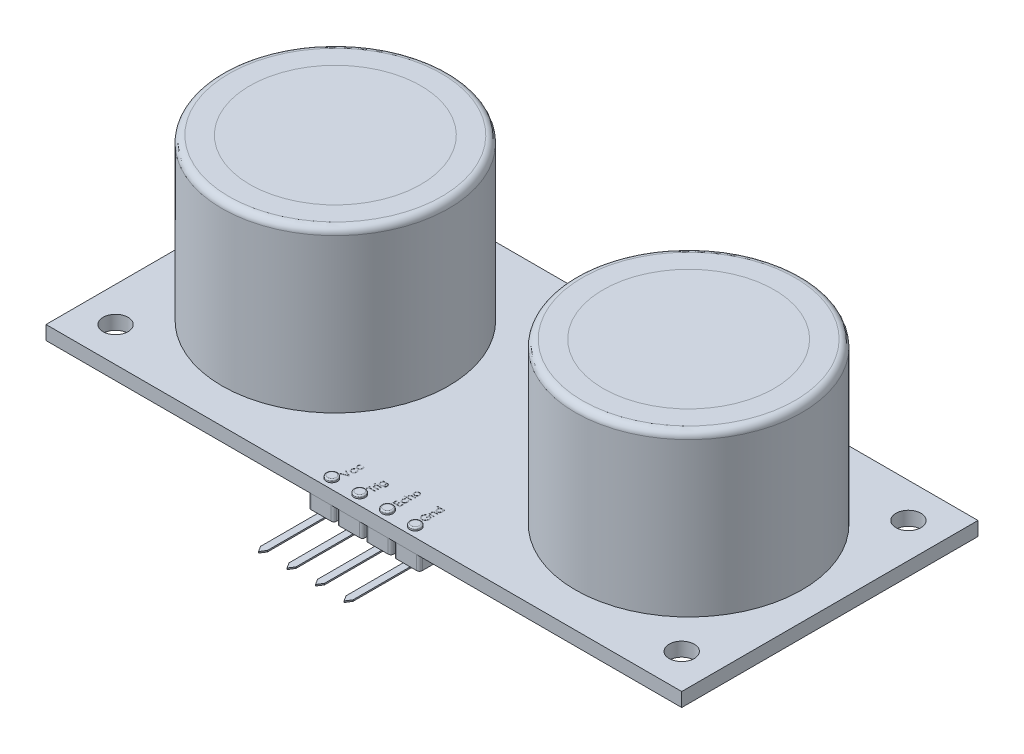
SolidWorks part; units mm, degrees
ref_plane "Front Plane" through (0, 0, 0) normal (0, 0, 1) x (1, 0, 0)
ref_plane "Top Plane" through (0, 0, 0) normal (0, 1, 0) x (1, 0, 0)
ref_plane "Right Plane" through (0, 0, 0) normal (1, 0, 0) x (0, 0, -1)
sketch "Sketch1" plane through (0, 0, 0) normal (0, 1, 0) x (1, 0, 0)
  line L1 (22.85, -10.65) -> (-22.85, -10.65)
  line L2 (22.85, -10.65) -> (22.85, 10.65)
  line L3 (22.85, 10.65) -> (-22.85, 10.65)
  line L4 (-22.85, -10.65) -> (-22.85, 10.65)
  line L5 (22.85, -10.65) -> (-22.85, 10.65) construction
  line L6 (22.85, 10.65) -> (-22.85, -10.65) construction
  line L7 (-20.35, -8.15) -> (20.35, -8.15) construction
  line L8 (-20.35, -8.15) -> (-20.35, 8.15) construction
  line L9 (-20.35, 8.15) -> (20.35, 8.15) construction
  line L10 (20.35, -8.15) -> (20.35, 8.15) construction
  circle A0 centre (20.35, 8.15) radius 0.9
  circle A1 centre (-20.35, -8.15) radius 0.9
  circle A2 centre (-20.35, 8.15) radius 0.9
  circle A3 centre (20.35, -8.15) radius 0.9
  point P0 (0, 0)
  dimension "D3" = 1.8
  dimension "D1" = 45.7
  dimension "D2" = 21.3
  dimension "D4" = 2.5
  dimension "D5" = 2.5
  dimension "D6" = 2.5
  dimension "D7" = 2.5
extrude "Boss-Extrude1" add sketch "Sketch1" along normal blind 1
sketch "Sketch2" plane through (0, 1, 0) normal (0, 1, 0) x (1, 0, 0)
  line L0 (0, 0) -> (0, -50000) construction
  circle A0 centre (-12.7, 0) radius 8.15
  circle A1 centre (12.7, 0) radius 8.15
  circle A2 centre (-12.7, 0) radius 6.15
  circle A3 centre (12.7, 0) radius 6.15
  point P4 (20.85, 0)
  point P6 (-20.85, 0)
  dimension "D1" = 16.3
  dimension "D2" = 41.7
  dimension "D3" = 20.85
  dimension "D4" = 2
extrude "Boss-Extrude2" add sketch "Sketch2" along normal blind 11.54 separate body
fillet "Fillet1" radius 0.5 1 edges at (-12.7, 12.54, 8.15)
fillet "Fillet2" radius 0.5 1 edges at (12.7, 12.54, 8.15)
sketch "Sketch3" plane through (0, 1, 0) normal (0, 1, 0) x (1, 0, 0)
  circle A0 centre (-12.7, 0) radius 6
  circle A1 centre (12.7, 0) radius 6
  dimension "D1" = 12
extrude "Boss-Extrude3" add sketch "Sketch3" along normal blind 7 separate body
ref_plane "Plane1" through (12.7, 0, 0) normal (1, 0, 0) x (0, 0, -1)
sketch "Sketch5" plane through (12.7, 0, 0) normal (1, 0, 0) x (0, 0, -1)
  line L0 (0, 8) -> (0, -49992) construction
  line L1 (6, 8) -> (-6, 8) construction
  line L2 (0.75, 8.5) -> (0.75, 8.4)
  line L4 (0.75, 8.5) -> (0, 8.5)
  line L5 (4, 8.915) -> (2, 8)
  line L6 (0.75, 8.4) -> (0.95, 8.4)
  line L7 (0, 8.5) -> (0, 8)
  line L8 (0, 8) -> (2, 8)
  line L9 (0.95, 8.4) -> (4, 8.915)
  point P4 (0, 8)
  dimension "D1" = 4
  dimension "D2" = 0.5
  dimension "D3" = 0.75
  dimension "D4" = 0.1
  dimension "D5" = 2
  dimension "D6" = 15
  dimension "D7" = 0.2
revolve "Revolve1" add sketch "Sketch5" angle 360 about L0
pattern_linear "LPattern2" count 2 spacing 25.4 along (-1, 0, 0) of "Revolve1"
sketch "Sketch6" plane through (0, 12.54, 0) normal (0, 1, 0) x (1, 0, 0)
  circle A0 centre (-12.7, 0) radius 6.15
  circle A1 centre (12.7, 0) radius 6.15
  dimension "D1" = 12.3
extrude "Boss-Extrude4" add sketch "Sketch6" against normal blind 0.2 separate body
sketch "Sketch18" plane through (0, 0, 0) normal (0, -1, 0) x (1, 0, 0)
  line L0 (-22.85, 10.65) -> (22.85, 10.65) construction
  line L1 (-3.8, 10.65) -> (-2.35, 10.65)
  line L2 (-4, 10.45) -> (-4, 8.85)
  line L3 (-3.8, 8.65) -> (-2.35, 8.65)
  line L4 (4, 10.45) -> (4, 8.85)
  line L5 (0, 8.65) -> (0, 10.65) construction
  line L6 (-4, 9.65) -> (4, 9.65) construction
  line L7 (0, 0) -> (0, 50000) construction
  line L8 (-2.15, 10.45) -> (-2.15, 8.85)
  line L9 (0.1, 10.45) -> (0.1, 8.85)
  line L10 (-1.95, 10.45) -> (-1.95, 8.85)
  line L11 (-1.75, 10.65) -> (-0.3, 10.65)
  line L12 (-1.75, 8.65) -> (-0.3, 8.65)
  line L13 (-0.1, 8.85) -> (-0.1, 10.45)
  line L14 (0.3, 10.65) -> (1.75, 10.65)
  line L15 (0.3, 8.65) -> (1.75, 8.65)
  line L16 (1.95, 10.45) -> (1.95, 8.85)
  line L17 (2.15, 10.45) -> (2.15, 8.85)
  line L18 (2.35, 10.65) -> (3.8, 10.65)
  line L19 (2.35, 8.65) -> (3.8, 8.65)
  arc A0 (3.8, 8.65) -> (4, 8.85) centre (3.8, 8.85) ccw
  arc A1 (4, 10.45) -> (3.8, 10.65) centre (3.8, 10.45) ccw
  arc A2 (2.15, 8.85) -> (2.35, 8.65) centre (2.35, 8.85) ccw
  arc A3 (2.15, 10.45) -> (2.35, 10.65) centre (2.35, 10.45) cw
  arc A4 (1.95, 8.85) -> (1.75, 8.65) centre (1.75, 8.85) cw
  arc A5 (1.95, 10.45) -> (1.75, 10.65) centre (1.75, 10.45) ccw
  arc A6 (0.1, 8.85) -> (0.3, 8.65) centre (0.3, 8.85) ccw
  arc A7 (0.1, 10.45) -> (0.3, 10.65) centre (0.3, 10.45) cw
  arc A8 (-0.1, 8.85) -> (-0.3, 8.65) centre (-0.3, 8.85) cw
  arc A9 (-0.1, 10.45) -> (-0.3, 10.65) centre (-0.3, 10.45) ccw
  arc A10 (-1.95, 10.45) -> (-1.75, 10.65) centre (-1.75, 10.45) cw
  arc A11 (-1.95, 8.85) -> (-1.75, 8.65) centre (-1.75, 8.85) ccw
  arc A12 (-2.35, 8.65) -> (-2.15, 8.85) centre (-2.35, 8.85) ccw
  arc A13 (-2.15, 10.45) -> (-2.35, 10.65) centre (-2.35, 10.45) ccw
  arc A14 (-4, 8.85) -> (-3.8, 8.65) centre (-3.8, 8.85) ccw
  arc A15 (-4, 10.45) -> (-3.8, 10.65) centre (-3.8, 10.45) cw
  point P24 (4, 10.65)
  point P27 (2.15, 8.65)
  point P30 (2.15, 10.65)
  point P33 (1.95, 8.65)
  point P38 (0.1, 8.65)
  point P41 (0.1, 10.65)
  point P46 (-0.1, 10.65)
  point P49 (-1.95, 10.65)
  point P52 (-1.95, 8.65)
  point P59 (-4, 8.65)
  point P62 (-4, 10.65)
  point P212 (0, 9.65)
extrude "Boss-Extrude10" add sketch "Sketch18" along normal blind 1 separate body
sketch "Sketch13" plane through (0, 1, 0) normal (0, 1, 0) x (1, 0, 0)
  line L0 (-4, -10.65) -> (-4, -8.7338) construction
  line L1 (-22.85, -10.65) -> (22.85, -10.65) construction
  line L2 (-4, -8.7338) -> (4, -8.7338) construction
  line L3 (4, -8.7338) -> (4, -10.65) construction
  line L4 (4, -10.65) -> (-4, -10.65) construction
  line L5 (0, 0) -> (0, -50000) construction
  circle A0 centre (-3, -9.95) radius 0.4
  circle A1 centre (-1, -9.95) radius 0.4
  circle A2 centre (1, -9.95) radius 0.4
  circle A3 centre (3, -9.95) radius 0.4
  point P9 (-4, -9.6919)
extrude "Boss-Extrude8" add sketch "Sketch13" along normal blind 0.2 separate body
fillet "Fillet3" radius 0.1 1 edges at (-3, 1.2, 10.35)
fillet "Fillet4" radius 0.1 1 edges at (-1, 1.2, 10.35)
fillet "Fillet5" radius 0.1 1 edges at (1, 1.2, 10.35)
fillet "Fillet6" radius 0.1 1 edges at (3, 1.2, 10.35)
sketch "Sketch15" plane through (0, 1, 0) normal (0, 1, 0) x (1, 0, 0)
  line L0 (-22.85, -10.65) -> (22.85, -10.65) construction
  line L1 (3.4865, -7.65) -> (-2.4849, -7.65) construction
  line L2 (3.4865, -7.65) -> (3.4865, -10.65) construction
  line L3 (3.4865, -10.65) -> (-2.4849, -10.65) construction
  line L5 (-2.4849, -7.65) -> (-2.4849, -10.65) construction
  line L6 (3.4865, -7.65) -> (-2.4849, -10.65) construction
  line L7 (3.4865, -10.65) -> (-2.4849, -7.65) construction
  text T0 "Vcc  \r\nTrig   \r\nEcho\r\nGnd " font "Century Gothic" height 0.5
  point P0 (0.5008, -9.15)
  dimension "D1" = 3
extrude "Cut-Extrude5" cut sketch "Sketch15" against normal blind 0.01
sketch "Sketch19" plane through (0, -1, 0) normal (0, -1, 0) x (1, 0, 0)
  line L1 (3.325, 9.15) -> (2.825, 9.15)
  line L2 (3.325, 9.15) -> (3.325, 14.75)
  line L3 (3.075, 15.15) -> (2.825, 15.15)
  line L4 (2.825, 9.15) -> (2.825, 14.75)
  line L5 (3.075, 15.15) -> (3.075, 9.15) construction
  line L6 (3.325, 12.15) -> (2.825, 12.15) construction
  line L7 (1.275, 9.15) -> (0.775, 9.15)
  line L8 (1.275, 9.15) -> (1.275, 14.75)
  line L9 (1.025, 15.15) -> (0.775, 15.15)
  line L10 (0.775, 9.15) -> (0.775, 14.75)
  line L11 (1.025, 15.15) -> (1.025, 9.15) construction
  line L12 (1.275, 12.15) -> (0.775, 12.15) construction
  line L13 (-0.775, 9.15) -> (-1.275, 9.15)
  line L14 (-0.775, 9.15) -> (-0.775, 14.75)
  line L15 (-1.025, 15.15) -> (-1.275, 15.15)
  line L16 (-1.275, 9.15) -> (-1.275, 14.75)
  line L17 (-1.025, 15.15) -> (-1.025, 9.15) construction
  line L18 (-0.775, 12.15) -> (-1.275, 12.15) construction
  line L19 (-2.825, 9.15) -> (-3.325, 9.15)
  line L20 (-2.825, 9.15) -> (-2.825, 14.75)
  line L21 (-3.075, 15.15) -> (-3.325, 15.15)
  line L22 (-3.325, 9.15) -> (-3.325, 14.75)
  line L23 (-3.075, 15.15) -> (-3.075, 9.15) construction
  line L24 (-2.825, 12.15) -> (-3.325, 12.15) construction
  line L26 (-1.75, 8.65) -> (-0.3, 8.65) construction
  line L27 (-3.8, 8.65) -> (-2.35, 8.65) construction
  line L29 (-3.075, 15.15) -> (-2.825, 14.75)
  line L30 (-3.075, 15.15) -> (-3.325, 14.75)
  line L31 (-1.025, 15.15) -> (-0.775, 14.75)
  line L32 (1.025, 15.15) -> (1.275, 14.75)
  line L33 (-1.275, 14.75) -> (-1.025, 15.15)
  line L34 (1.025, 15.15) -> (0.775, 14.75)
  line L35 (3.075, 15.15) -> (3.325, 14.75)
  line L37 (2.825, 14.75) -> (3.075, 15.15)
  point P20 (-1.025, 8.65)
  point P23 (-3.075, 8.65)
  point P300 (-1.025, 12.15)
  point P301 (-3.075, 12.15)
  point P352 (1.025, 12.15)
  point P420 (3.075, 12.15)
  dimension "D2" = 6
  dimension "D3" = 0.5
  dimension "D4" = 0.5
  dimension "D5" = 0.5
  dimension "D6" = 0.5
  dimension "D7" = 0.4
  dimension "D8" = 0.4
  dimension "D9" = 0.4717
extrude "Boss-Extrude11" add sketch "Sketch19" along normal blind 0.1 separate body contours L29 L20 L19 L22 L30 | L31 L14 L13 L16 L33 | L32 L8 L7 L10 L34 | L35 L2 L1 L4 L37
sketch "Sketch21" plane through (0, 1, 0) normal (0, 1, 0) x (1, 0, 0)
  line L0 (22.85, 10.65) -> (-22.85, 10.65) construction
  line L1 (3, 6.65) -> (-3, 6.65)
  line L3 (3, 9.65) -> (-3, 9.65)
  arc A0 (-3, 9.65) -> (-3, 6.65) centre (-3, 8.15) ccw
  arc A1 (3, 6.65) -> (3, 9.65) centre (3, 8.15) ccw
  point P14 (-4.5, 8.15)
  point P16 (4.5, 8.15)
  dimension "D1" = 3
  dimension "D2" = 6
  dimension "D3" = 1
extrude "Boss-Extrude13" add sketch "Sketch21" along normal blind 0.5 separate body
sketch "Sketch22" plane through (0, 1.5, 0) normal (0, 1, 0) x (1, 0, 0)
  line L1 (-2.9874, 7.15) -> (3, 7.15)
  line L3 (-3, 9.15) -> (3, 9.15)
  line L4 (-3, 6.65) -> (3, 6.65) construction
  arc A0 (-3, 9.15) -> (-2.9874, 7.15) centre (-3, 8.15) ccw
  arc A1 (3, 7.15) -> (3, 9.15) centre (3, 8.15) ccw
  arc A2 (-3, 9.65) -> (-3, 6.65) centre (-3, 8.15) ccw construction
  arc A3 (3, 6.65) -> (3, 9.65) centre (3, 8.15) ccw construction
  point P2 (4.5, 8.15)
  point P3 (4, 8.15)
  point P4 (-4.5, 8.15)
  point P5 (-4, 8.1437)
  dimension "D1" = 0.5
  dimension "D3" = 1
  dimension "D2" = 2
  dimension "D4" = 0.5
  dimension "D5" = 0.5
extrude "Boss-Extrude14" add sketch "Sketch22" along normal blind 1.5
fillet "Fillet7" radius 0.1 8 edges at (-4, 3, -8.1437) (0, 3, -9.15) (4, 3, -8.15) (-4.5, 1.5, -8.15) (0, 1.5, -9.65) (4.5, 1.5, -8.15) (0.0063, 3, -7.15) (0, 1.5, -6.65)
equation "\"D2@Sketch13\"=\"D1@Sketch13\"/2"
equation "\"D9@Sketch18\"=\"D1@Sketch18\"/2"
